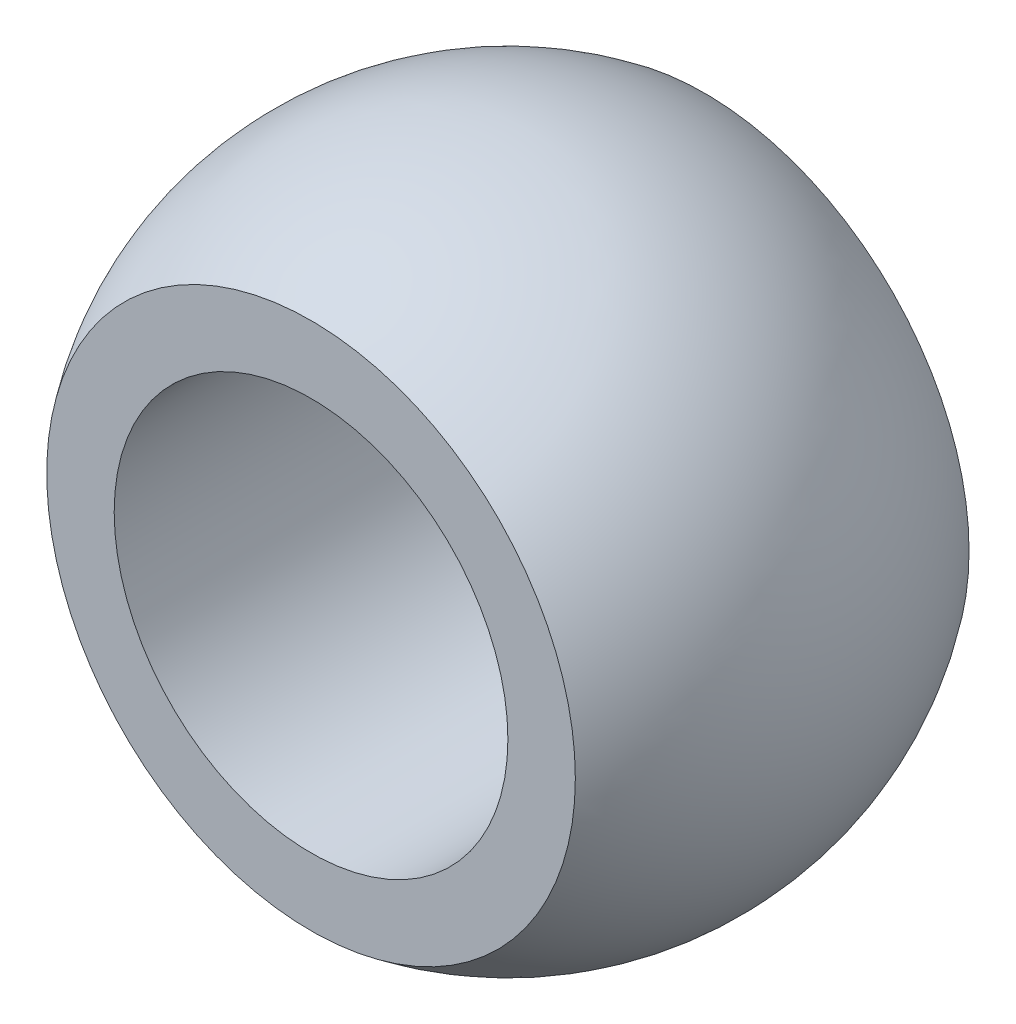
SolidWorks part; units mm, degrees
ref_plane "Front Plane" through (0, 0, 0) normal (0, 0, 1) x (1, 0, 0)
ref_plane "Top Plane" through (0, 0, 0) normal (0, 1, 0) x (1, 0, 0)
ref_plane "Right Plane" through (0, 0, 0) normal (1, 0, 0) x (0, 0, -1)
sketch "Sketch1" plane through (0, 0, 0) normal (0, 0, 1) x (1, 0, 0)
  line L0 (0, 2.3813) -> (0, -2.3813)
  line L1 (0, 0) -> (2.3813, 0) construction
  arc A0 (0, 2.3813) -> (0, -2.3813) centre (0, 0) cw
ref_plane "Plane1" through (0, 0, 0) normal (0, 0, 1) x (1, 0, 0)
sketch "Sketch2" plane through (0, 0, 0) normal (0, 0, 1) x (1, 0, 0)
  line L0 (0, 2.3813) -> (0, -2.3813)
  arc A0 (0, 2.3813) -> (0, -2.3813) centre (0, 0) cw
  arc A1 (0, -2.3813) -> (0, 2.3813) centre (0, 0) ccw construction
revolve "Revolve2" add sketch "Sketch2" angle 360 about L0
sketch "Sketch4" plane through (0, 0, 0) normal (0, 0, 1) x (1, 0, 0)
  circle A0 centre (0, 0) radius 1.4224
extrude "Extrude1" cut sketch "Sketch4" along normal through all and the other way through all
ref_plane "Plane4" through (0, 0, 1.4224) normal (0, 0, 1) x (1, 0, 0)
ref_plane "Plane5" through (0, 0, -1.4224) normal (0, 0, 1) x (1, 0, 0)
sketch "Sketch5" plane through (0, 0, -1.4224) normal (0, 0, 1) x (1, 0, 0)
  line L0 (0, 2.3813) -> (0, -2.3813) construction
  circle A0 centre (0, 0) radius 1.4224
extrude "Extrude2" cut sketch "Sketch5" against normal blind 2.54 flip side to cut
sketch "Sketch6" plane through (0, 0, 1.4224) normal (0, 0, 1) x (1, 0, 0)
  circle A0 centre (0, 0) radius 1.4224
extrude "Extrude3" cut sketch "Sketch6" along normal blind 2.54 flip side to cut
